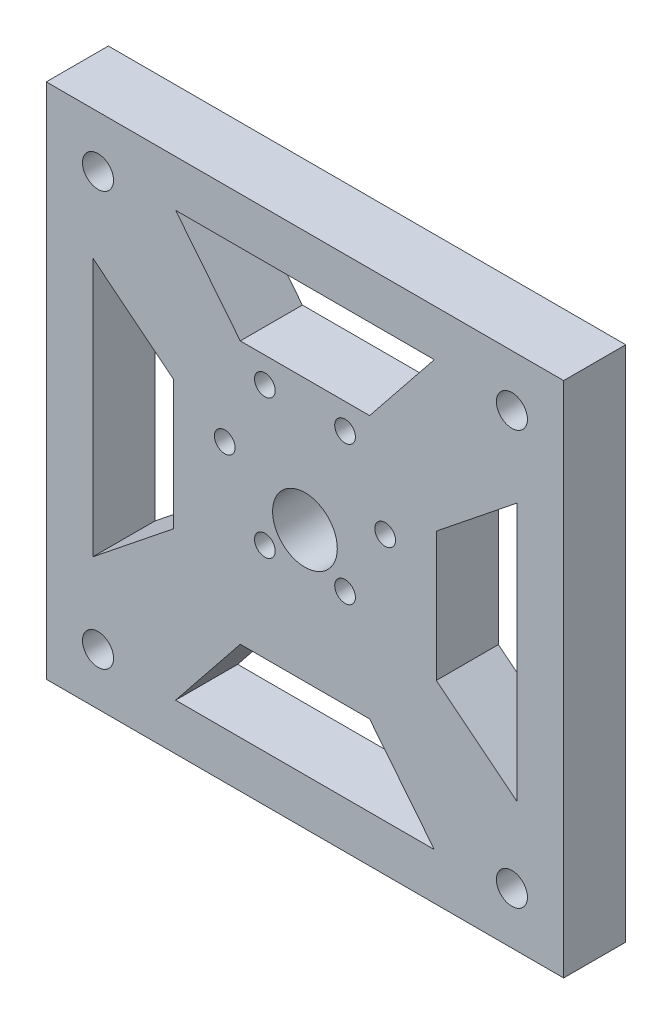
SolidWorks part; units mm, degrees
ref_plane "Plan de face" through (0, 0, 0) normal (0, 0, 1) x (1, 0, 0)
ref_plane "Plan de dessus" through (0, 0, 0) normal (0, 1, 0) x (1, 0, 0)
ref_plane "Plan de droite" through (0, 0, 0) normal (1, 0, 0) x (0, 0, -1)
sketch "Esquisse1" plane through (0, 0, 0) normal (0, 0, 1) x (1, 0, 0)
  circle A0 centre (0, 0) radius 18.5
  dimension "D1" = 37
extrude "Boss.-Extru.1" add sketch "Esquisse1" along normal blind 12
sketch "Esquisse2" plane through (0, 0, 12) normal (0, 0, 1) x (1, 0, 0)
  line L0 (-18.5, 0) -> (18.5, 0) construction
  circle A0 centre (0, 0) radius 18.5 construction
  circle A1 centre (-15.5, 0) radius 2
  circle A2 centre (15.5, 0) radius 2
  circle A3 centre (7.75, -13.4234) radius 2
  circle A4 centre (-7.75, -13.4234) radius 2
  circle A5 centre (-15.5, 0) radius 2
  circle A6 centre (-7.75, 13.4234) radius 2
  circle A7 centre (7.75, 13.4234) radius 2
  point P22 (0, 0)
  dimension "D1" = 31
  dimension "D2" = 15.5
  dimension "D3" = 4
  dimension "D4" = 4
  dimension "D5" = 6
extrude "Enlèv. mat.-Extru.1" cut sketch "Esquisse2" against normal through all contours A6 | A7 | A2 L0 | L0 A2 | A3 | A4 | L0 A5 | A1 L0
sketch "Esquisse3" plane through (0, 0, 12) normal (0, 0, 1) x (1, 0, 0)
  circle A0 centre (0, -7) radius 6.25
  dimension "D1" = 12.5
  dimension "D3" = 7
extrude "Enlèv. mat.-Extru.2" cut sketch "Esquisse3" against normal through all
sketch "Esquisse4" plane through (0, 0, 12) normal (0, 0, 1) x (1, 0, 0)
  line L1 (50, 43) -> (-50, 43)
  line L2 (50, 43) -> (50, -57)
  line L3 (50, -57) -> (-50, -57)
  line L4 (-50, 43) -> (-50, -57)
  line L5 (50, 43) -> (-50, -57) construction
  line L6 (50, -57) -> (-50, 43) construction
  circle A0 centre (0, 0) radius 18.5
  point P3 (0, -7)
  dimension "D1" = 100
  dimension "D2" = 100
extrude "Boss.-Extru.2" add sketch "Esquisse4" against normal blind 12 contours L2 L1 L4 L3 | A0
sketch "Esquisse5" plane through (0, 0, 12) normal (0, 0, 1) x (1, 0, 0)
  line L0 (50, 43) -> (-50, 43) construction
  line L1 (-50, 43) -> (-50, -57) construction
  circle A0 centre (-40, 33) radius 3
  circle A1 centre (40, 33) radius 3
  circle A2 centre (40, -47) radius 3
  circle A3 centre (-40, -47) radius 3
  dimension "D1" = 6
  dimension "D2" = 10
  dimension "D3" = 10
  dimension "D4" = 2
  dimension "D5" = 2
extrude "Enlèv. mat.-Extru.3" cut sketch "Esquisse5" against normal blind 12
sketch "Esquisse6" plane through (0, 0, 12) normal (0, 0, 1) x (1, 0, 0)
  line L0 (-41, 18) -> (-41, -32)
  line L1 (-41, -32) -> (-25.3875, -19.5)
  line L2 (-25.3875, -19.5) -> (-25.3875, 5.5)
  line L3 (-25.3875, 5.5) -> (-41, 18)
  line L4 (-50, 43) -> (-50, -57) construction
  line L5 (50, 43) -> (-50, 43) construction
  line L6 (12.5, 18.3875) -> (25, 34)
  line L7 (25, 34) -> (-25, 34)
  line L8 (-25, 34) -> (-12.5, 18.3875)
  line L9 (-12.5, 18.3875) -> (12.5, 18.3875)
  line L10 (25.3875, -19.5) -> (41, -32)
  line L11 (41, -32) -> (41, 18)
  line L12 (41, 18) -> (25.3875, 5.5)
  line L13 (25.3875, 5.5) -> (25.3875, -19.5)
  line L14 (-12.5, -32.3875) -> (-25, -48)
  line L15 (-25, -48) -> (25, -48)
  line L16 (25, -48) -> (12.5, -32.3875)
  line L17 (12.5, -32.3875) -> (-12.5, -32.3875)
  point P23 (0, -7)
  dimension "D1" = 50
  dimension "D2" = 25
  dimension "D3" = 20
  dimension "D4" = 20
  dimension "D5" = 9
  dimension "D6" = 25
  dimension "D7" = 4
extrude "Enlèv. mat.-Extru.4" cut sketch "Esquisse6" against normal blind 12
